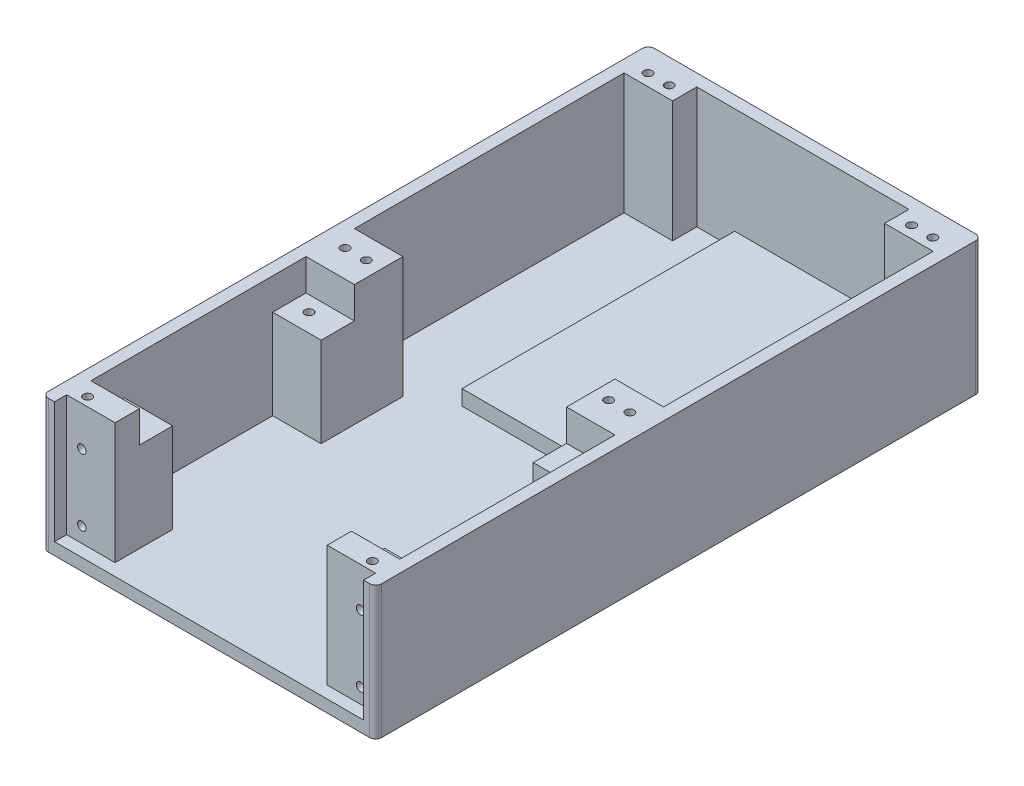
SolidWorks part; units mm, degrees
ref_plane "Front Plane" through (0, 0, 0) normal (0, 0, 1) x (1, 0, 0)
ref_plane "Top Plane" through (0, 0, 0) normal (0, 1, 0) x (1, 0, 0)
ref_plane "Right Plane" through (0, 0, 0) normal (1, 0, 0) x (0, 0, -1)
sketch "Sketch1" plane through (0, 0, 0) normal (0, 1, 0) x (1, 0, 0)
  line L1 (0, 0) -> (139.7, 0)
  line L2 (0, 0) -> (0, 254)
  line L3 (0, 254) -> (139.7, 254)
  line L4 (139.7, 0) -> (139.7, 254)
  dimension "D1" = 254
  dimension "D2" = 139.7
extrude "Base" add sketch "Sketch1" along normal blind 5.08
sketch "Sketch2" plane through (0, 5.08, 0) normal (0, 1, 0) x (1, 0, 0)
  line L1 (0, 254) -> (139.7, 254)
  line L2 (0, 254) -> (0, 0)
  line L3 (0, 0) -> (139.7, 0)
  line L4 (139.7, 254) -> (139.7, 0)
  line L5 (5.08, 248.92) -> (134.62, 248.92)
  line L6 (5.08, 248.92) -> (5.08, 5.08)
  line L7 (5.08, 5.08) -> (134.62, 5.08)
  line L8 (134.62, 248.92) -> (134.62, 5.08)
  line M9 (0, 254) -> (0, 0)
  line M10 (0, 0) -> (139.7, 0)
  line M11 (139.7, 0) -> (139.7, 254)
  line M12 (139.7, 254) -> (0, 254)
  dimension "D1" = 5.08
  dimension "D2" = 5.08
  dimension "D3" = 5.08
  dimension "D4" = 5.08
extrude "Walls" add sketch "Sketch2" along normal blind 50.8 contours L5 L8 L7 L6 M12 M9 M10 M11
ref_plane "Plane1" through (0, 0, -60.96) normal (0, 0, 1) x (1, 0, 0)
sketch "Sketch4" plane through (0, 0, 0) normal (0, 0, 1) x (1, 0, 0)
  line L0 (0, 0) -> (139.7, 0) construction
  line L1 (5.08, 55.88) -> (134.62, 55.88)
  line L2 (5.08, 55.88) -> (5.08, 5.08)
  line L3 (5.08, 5.08) -> (134.62, 5.08)
  line L4 (134.62, 55.88) -> (134.62, 5.08)
  line L5 (0, 55.88) -> (0, 0) construction
  line L6 (139.7, 55.88) -> (139.7, 0) construction
  line L7 (0, 55.88) -> (139.7, 55.88) construction
  dimension "D1" = 5.08
  dimension "D2" = 5.08
  dimension "D3" = 5.08
  dimension "D4" = 0
extrude "Bottom Cut" cut sketch "Sketch4" against normal blind 139.7
sketch "Sketch12" plane through (0, 5.08, 0) normal (0, 1, 0) x (1, 0, 0)
  line L0 (139.7, 254) -> (0, 254) construction
  line L1 (134.62, 248.92) -> (114.3, 248.92)
  line L2 (134.62, 248.92) -> (134.62, 238.76)
  line L3 (134.62, 238.76) -> (114.3, 238.76)
  line L4 (114.3, 248.92) -> (114.3, 238.76)
  line L5 (139.7, 0) -> (139.7, 254) construction
  line L7 (5.08, 248.92) -> (25.4, 248.92)
  line L8 (5.08, 248.92) -> (5.08, 238.76)
  line L9 (5.08, 238.76) -> (25.4, 238.76)
  line L10 (25.4, 248.92) -> (25.4, 238.76)
  line L11 (134.62, 105.41) -> (114.3, 105.41)
  line L12 (134.62, 105.41) -> (134.62, 125.73)
  line L13 (134.62, 125.73) -> (114.3, 125.73)
  line L14 (114.3, 105.41) -> (114.3, 125.73)
  line L15 (5.08, 105.41) -> (25.4, 105.41)
  line L16 (5.08, 105.41) -> (5.08, 125.73)
  line L17 (5.08, 125.73) -> (25.4, 125.73)
  line L18 (25.4, 105.41) -> (25.4, 125.73)
  dimension "D1" = 15.24
  dimension "D2" = 25.4
  dimension "D3" = 20.32
extrude "Mounting Struts" add sketch "Sketch12" along normal up to surface (50.8 mm away) up to face at (69.85, 55.88, -125.73)
sketch "Sketch13" plane through (0, 55.88, 0) normal (0, 1, 0) x (1, 0, 0)
  line L0 (139.7, 254) -> (0, 254) construction
  line L1 (139.7, 0) -> (139.7, 254) construction
  circle A0 centre (120.65, 243.713) radius 1.778
  circle A1 centre (19.05, 243.713) radius 1.778
  circle A2 centre (120.65, 116.713) radius 1.778
  circle A3 centre (19.05, 116.713) radius 1.778
  dimension "D1" = 3.556
  dimension "D2" = 10.287
  dimension "D3" = 19.05
  dimension "D4" = 101.6
  dimension "D5" = 127
extrude "Panel Mounting Holes" cut sketch "Sketch13" against normal blind 12.7
sketch "Sketch14" plane through (0, 53.848, 0) normal (0, 1, 0) x (1, 0, 0)
  line L1 (134.62, 5.08) -> (114.3, 5.08)
  line L2 (134.62, 5.08) -> (134.62, 15.24)
  line L3 (134.62, 15.24) -> (114.3, 15.24)
  line L4 (114.3, 5.08) -> (114.3, 15.24)
  line L5 (5.08, 5.08) -> (25.4, 5.08)
  line L6 (5.08, 5.08) -> (5.08, 15.24)
  line L7 (5.08, 15.24) -> (25.4, 15.24)
  line L8 (25.4, 5.08) -> (25.4, 15.24)
  dimension "D1" = 10.16
  dimension "D2" = 20.32
extrude "Boss-Extrude6" add sketch "Sketch14" along normal up to surface and the other way up to surface
sketch "Sketch17" plane through (0, 55.88, 0) normal (0, 1, 0) x (1, 0, 0)
  line L0 (139.7, 0) -> (139.7, 254) construction
  line L1 (0, -30.734) -> (0, 30.734) construction
  circle A0 centre (129.54, 243.713) radius 1.778
  circle A1 centre (10.16, 243.713) radius 1.778
  circle A2 centre (10.16, 116.713) radius 1.778
  circle A3 centre (129.54, 116.713) radius 1.778
  circle A4 centre (129.54, 8.763) radius 1.778
  circle A5 centre (10.16, 8.763) radius 1.778
  circle A7 centre (120.65, 116.713) radius 1.778 construction
  circle A8 centre (19.05, 116.713) radius 1.778 construction
  circle A9 centre (19.05, 243.713) radius 1.778 construction
  circle A10 centre (120.65, 243.713) radius 1.778 construction
  dimension "D1" = 3.556
  dimension "D2" = 10.16
  dimension "D3" = 10.16
  dimension "D4" = 127
  dimension "D5" = 107.95
extrude "Front Mounting Holes" cut sketch "Sketch17" against normal blind 12.7
fillet "Corner Fillet" radius 2.54 4 edges at (0, 27.94, 0) (139.7, 27.94, 0) (0, 27.94, -254) (139.7, 27.94, -254)
sketch "Sketch18" plane through (0, 5.08, 0) normal (0, 1, 0) x (1, 0, 0)
  line L0 (25.4, 105.41) -> (25.4, 125.73) construction
  line L1 (5.08, 105.41) -> (25.4, 105.41)
  line L2 (5.08, 105.41) -> (5.08, 91.44)
  line L3 (5.08, 91.44) -> (25.4, 91.44)
  line L4 (25.4, 105.41) -> (25.4, 91.44)
  line L5 (134.62, 105.41) -> (114.3, 105.41)
  line L6 (134.62, 105.41) -> (134.62, 91.44)
  line L7 (134.62, 91.44) -> (114.3, 91.44)
  line L8 (114.3, 105.41) -> (114.3, 91.44)
  line L9 (134.62, 15.24) -> (114.3, 15.24)
  line L10 (134.62, 15.24) -> (134.62, 29.21)
  line L11 (134.62, 29.21) -> (114.3, 29.21)
  line L12 (114.3, 15.24) -> (114.3, 29.21)
  line L13 (5.08, 15.24) -> (25.4, 15.24)
  line L14 (5.08, 15.24) -> (5.08, 29.21)
  line L15 (5.08, 29.21) -> (25.4, 29.21)
  line L16 (25.4, 15.24) -> (25.4, 29.21)
  line L17 (114.3, 125.73) -> (114.3, 105.41) construction
  dimension "D1" = 13.97
extrude "Insert Mount" add sketch "Sketch18" along normal blind 37.592
sketch "Sketch19" plane through (0, 42.672, 0) normal (0, 1, 0) x (1, 0, 0)
  line L0 (114.3, 105.41) -> (134.62, 105.41) construction
  line L1 (134.62, 105.41) -> (134.62, 15.24) construction
  line L2 (5.08, 15.24) -> (25.4, 15.24) construction
  line L3 (5.08, 105.41) -> (5.08, 15.24) construction
  circle A0 centre (12.7, 99.06) radius 1.778
  circle A1 centre (127, 99.06) radius 1.778
  circle A2 centre (127, 21.59) radius 1.778
  circle A3 centre (12.7, 21.59) radius 1.778
  dimension "D1" = 3.556
  dimension "D2" = 6.35
  dimension "D3" = 7.62
  dimension "D4" = 6.35
  dimension "D5" = 7.62
extrude "Cut-Extrude1" cut sketch "Sketch19" against normal blind 12.7
sketch "Sketch20" plane through (0, 5.08, 0) normal (0, 1, 0) x (1, 0, 0)
  line L0 (25.4, 248.92) -> (114.3, 248.92) construction
  line L1 (98.425, 248.92) -> (41.275, 248.92)
  line L2 (98.425, 248.92) -> (98.425, 134.62)
  line L3 (98.425, 134.62) -> (41.275, 134.62)
  line L4 (41.275, 248.92) -> (41.275, 134.62)
  line L6 (25.4, 238.76) -> (114.3, 238.76) construction
  point P10 (69.85, 238.76)
  point P11 (69.85, 248.92)
  dimension "D1" = 57.15
  dimension "D2" = 114.3
other "AlignGroup1"
extrude "Arduino Mount" add sketch "Sketch20" along normal blind 6.35
sketch "Sketch21" plane through (0, 0, -5.08) normal (0, 0, 1) x (1, 0, 0)
  line L1 (5.08, 5.08) -> (134.62, 5.08) construction
  line L2 (134.62, 5.08) -> (134.62, 55.88) construction
  line L3 (5.08, 55.88) -> (5.08, 5.08) construction
  circle A0 centre (128.27, 11.43) radius 1.778
  circle A1 centre (128.27, 39.37) radius 1.778
  circle A2 centre (11.43, 39.37) radius 1.778
  circle A3 centre (11.43, 11.43) radius 1.778
  point P12 (126.6975, 44.2878)
  point P15 (0, 0)
  point P16 (0, 0)
  point P17 (0, 0)
  point P18 (0, 0)
  dimension "D1" = 3.556
  dimension "D2" = 6.35
  dimension "D3" = 27.94
  dimension "D4" = 6.35
  dimension "D5" = 6.35
extrude "Cut-Extrude2" cut sketch "Sketch21" against normal blind 7.62
equation "\"Arrow Height\"= 1.5in"
equation "\"Button Height\"= 2in"
equation "\"Button Width\"= 4in"
equation "\"Haptic Diameter\"= 10mm"
equation "\"Haptic Thickness\"= 2.7mm"
equation "\"Arrow Spacing\"= 1in"
equation "\"Arrow Width\"= 1in"
equation "\"Haptic Wire Angle\"= 63.43"
equation "\"Haptic Wire Width\"= .1in"
equation "\"Haptic Wire Height\"= .15in"
equation "\"Mounting Bolt Hole Diameter\"= .14in"
equation "\"D1@Sketch13\"=\"Mounting Bolt Hole Diameter\""
equation "\"D1@Sketch17\"=\"Mounting Bolt Hole Diameter\""
equation "\"D1@Sketch19\"=\"Mounting Bolt Hole Diameter\""
